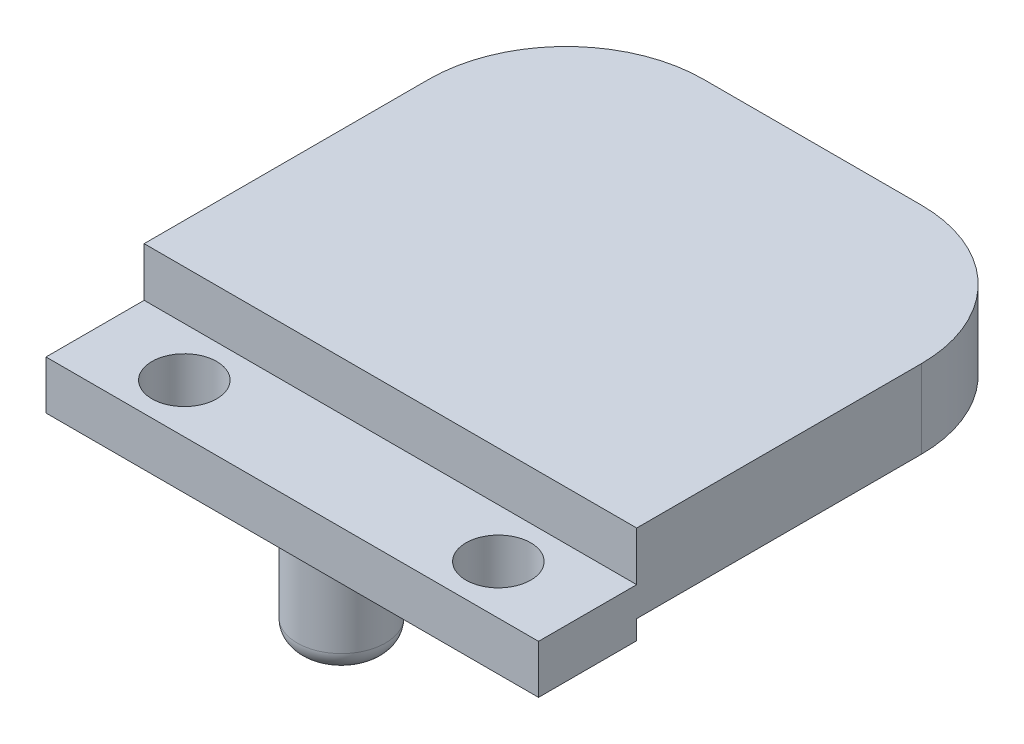
SolidWorks part; units mm, degrees
ref_plane "Front Plane" through (0, 0, 0) normal (0, 0, 1) x (1, 0, 0)
ref_plane "Top Plane" through (0, 0, 0) normal (0, 1, 0) x (1, 0, 0)
ref_plane "Right Plane" through (0, 0, 0) normal (1, 0, 0) x (0, 0, -1)
sketch "Sketch4" plane through (0, 0, 0) normal (0, 0, 1) x (1, 0, 0)
  line L1 (-6.23, -9.975) -> (6.23, -9.975)
  line L2 (-6.23, -9.975) -> (-6.23, 7.275)
  line L3 (-6.23, 7.275) -> (6.23, 7.275)
  line L4 (6.23, -9.975) -> (6.23, 7.275)
  point P4 (0, 7.275)
  dimension "D1" = 12.46
  dimension "D2" = 17.25
  dimension "D3" = 9.975
extrude "Boss-Extrude3" add sketch "Sketch4" along normal blind 6
sketch "Sketch8" plane through (0, -9.975, 0) normal (0, -1, 0) x (-1, 0, 0)
  circle A0 centre (0, -23.55) radius 12.5468
  circle A1 centre (0, -23.55) radius 11.15
  dimension "D1" = 22.3
  dimension "D2" = 23.55
extrude "Boss-Extrude6" add sketch "Sketch8" along normal blind 8.3 and the other way up to surface (17.25 mm away) other way up to face at (0, 7.275, 3)
sketch "Sketch5" plane through (0, 7.275, 0) normal (0, 1, 0) x (1, 0, 0)
  line L8 (12.5468, -23.55) -> (12.5468, 0)
  line L9 (12.5468, 0) -> (6.23, 0)
  line L10 (-12.5468, -23.55) -> (-12.5468, 0)
  line L11 (-12.5468, 0) -> (-6.23, 0)
  line L12 (-6.23, 0) -> (-6.23, -29.7)
  line L14 (6.23, -29.7) -> (6.23, 0)
  line L15 (-6.23, -29.7) -> (6.23, -29.7)
  line L16 (6.23, -6) -> (-6.23, -6) construction
  circle A0 centre (0, -23.55) radius 12.5468 construction
  arc A1 (-12.5468, -23.55) -> (12.5468, -23.55) centre (0, -23.55) ccw
  dimension "D1" = 23.7
  dimension "D2" = 23.55
extrude "Boss-Extrude4" add sketch "Sketch5" against normal up to surface (17.25 mm away) up to face at (0, -9.975, 3)
sketch "Sketch6" plane through (0, 7.275, 0) normal (0, 1, 0) x (1, 0, 0)
  line L0 (6.23, -6) -> (-6.23, -6) construction
  line L3 (6.23, -29.7) -> (-6.23, -29.7) construction
  circle A0 centre (0, -3.6) radius 0.75
  circle A1 centre (0, -32.1) radius 0.75
  dimension "D1" = 1.5
  dimension "D3" = 1.5
  dimension "D2" = 2.4
  dimension "D4" = 2.4
extrude "Cut-Extrude1" cut sketch "Sketch6" against normal blind 5
chamfer "Chamfer1" distance 0.5 angle 60 2 edges at (0, 7.275, 4.35) (0, 7.275, 32.85)
sketch "Sketch10" plane through (0, 7.275, 0) normal (0, 1, 0) x (1, 0, 0)
  line L1 (-6.23, -6) -> (6.23, -6)
  line L2 (-6.23, -6) -> (-6.23, -29.7)
  line L3 (-6.23, -29.7) -> (6.23, -29.7)
  line L4 (6.23, -6) -> (6.23, -29.7)
extrude "Cut-Extrude3" cut sketch "Sketch10" against normal up to surface (17.25 mm away) up to face at (0, -9.975, 10.3399)
ref_plane "Plane1" through (0, 0, 36.0968) normal (0, 0, 1) x (1, 0, 0)
sketch "Sketch13" plane through (0, -18.275, 0) normal (0, -1, 0) x (1, 0, 0)
  line L0 (-12.5468, 23.55) -> (-12.5468, 0)
  line L1 (-12.5468, 0) -> (12.5468, 0)
  line L2 (12.5468, 0) -> (12.5468, 23.55)
  arc A0 (-12.5468, 23.55) -> (12.5468, 23.55) centre (0, 23.55) ccw
  point P3 (0, 0)
extrude "Boss-Extrude7" add sketch "Sketch13" against normal up to surface (8.3 mm away) up to face at (0, -9.975, 10.3399)
sketch "Sketch15" plane through (0, 7.275, 0) normal (0, 1, 0) x (1, 0, 0)
  line L0 (-12.5468, 0) -> (12.5468, 0)
  line L1 (12.5468, 0) -> (12.5468, -23.55)
  line L2 (-12.5468, 0) -> (-12.5468, -23.55)
  line L3 (6.23, -6) -> (6.23, -29.7) construction
  line L4 (-6.23, -0.8) -> (6.23, -0.8)
  line L5 (-6.23, -0.8) -> (-6.23, -33)
  line L6 (-4.73, -34.5) -> (4.73, -34.5)
  line L7 (6.23, -0.8) -> (6.23, -33)
  arc A0 (-12.5468, -23.55) -> (12.5468, -23.55) centre (0, -23.55) ccw
  circle A1 centre (0, -3.6) radius 0.75 construction
  arc A2 (4.73, -34.5) -> (6.23, -33) centre (4.73, -33) ccw
  arc A3 (-6.23, -33) -> (-4.73, -34.5) centre (-4.73, -33) ccw
  point P15 (0, -0.8)
  dimension "D1" = 0.8
  dimension "D3" = 1.5
  dimension "D2" = 2.8
  dimension "D4" = 0
  dimension "D5" = 34.5
extrude "Boss-Extrude9" add sketch "Sketch15" along normal blind 10
sketch "Sketch20" plane through (0, -18.275, 0) normal (0, -1, 0) x (1, 0, 0)
  circle A0 centre (0, 23.55) radius 7.15
  circle A1 centre (0, 23.55) radius 11.15
  circle A2 centre (0, 23.55) radius 11.15 construction
  dimension "D1" = 14.3
extrude "Boss-Extrude11" add sketch "Sketch20" against normal up to surface (8.3 mm away) up to face at (0, -9.975, 27.1007)
sketch "Sketch21" plane through (0, -18.275, 0) normal (0, -1, 0) x (1, 0, 0)
  circle A0 centre (0, 23.55) radius 7.15
  circle A1 centre (0, 23.55) radius 10.15
  circle A2 centre (0, 23.55) radius 7.15 construction
  dimension "D1" = 20.3
extrude "Cut-Extrude7" cut sketch "Sketch21" against normal blind 1.3
sketch "Sketch11" plane through (0, 0, 29.7) normal (0, 0, 1) x (1, 0, 0)
  line L1 (-5, -9.975) -> (5, -9.975)
  line L2 (-5, -9.975) -> (-5, -11.975)
  line L3 (-5, -11.975) -> (5, -11.975)
  line L4 (5, -9.975) -> (5, -11.975)
  line L5 (3.6469, -9.975) -> (6.23, -9.975) construction
  point P4 (0, -9.975)
  dimension "D1" = 0
  dimension "D2" = 10
  dimension "D3" = 2
extrude "Cut-Extrude4" cut sketch "Sketch11" against normal up to surface (23.7 mm away) up to face at (0, -1.35, 6)
sketch "Sketch24" plane through (0, -18.275, 0) normal (0, -1, 0) x (1, 0, 0)
  line L0 (6.23, 20.0415) -> (6.23, 6) construction
  line L1 (-6.23, 6) -> (6.23, 6)
  line L2 (-6.23, 6) -> (-6.23, 12)
  line L3 (-6.23, 12) -> (6.23, 12)
  line L4 (6.23, 6) -> (6.23, 12)
  dimension "D1" = 6
extrude "Cut-Extrude8" cut sketch "Sketch24" against normal up to next
sketch "Sketch17" plane through (-12.5468, 4.7282, 0) normal (1, 0, 0) x (0, -1, 0)
  line L0 (26.9782, 26.5) -> (26.9782, 0)
  line L1 (26.9782, 0) -> (-17.5218, 0)
  line L2 (-17.5218, 0) -> (-17.5218, 26.5)
  line L3 (-17.5218, 26.5) -> (-13.5218, 26.5)
  line L4 (-13.5218, 26.5) -> (-13.5218, 5)
  line L5 (-13.5218, 5) -> (22.9782, 5)
  line L6 (22.9782, 5) -> (22.9782, 26.5)
  line L7 (22.9782, 26.5) -> (26.9782, 26.5)
  point P2 (4.7282, 5)
  point P10 (4.7282, 0)
  dimension "D1" = 4
  dimension "D2" = 36.5
  dimension "D3" = 0
  dimension "D4" = 26.5
  dimension "D5" = 5
extrude "Boss-Extrude10" add sketch "Sketch17" along normal up to surface (25.0936 mm away) up to face at (12.5468, -0.5, 11.775)
sketch "Sketch18" plane through (0, -18.25, 0) normal (0, 1, 0) x (0, 0, 1)
  line L0 (-26.5, -12.5468) -> (-26.5, 12.5468) construction
  line L1 (-26.5, 6.2191) -> (-5, 6.2191)
  line L2 (-26.5, 6.2191) -> (-26.5, -6.2191)
  line L3 (-26.5, -6.2191) -> (-5, -6.2191)
  line L4 (-5, 6.2191) -> (-5, -6.2191)
  line L5 (-5, -12.5468) -> (-5, 12.5468) construction
  point P6 (-26.5, 0)
  point P7 (-26.5, 0)
  dimension "D1" = 0
extrude "Cut-Extrude5" cut sketch "Sketch18" against normal blind 2
sketch "Sketch19" plane through (0, -20.25, 0) normal (0, 1, 0) x (0, 0, 1)
  line L0 (-26.5, -12.5468) -> (-26.5, 12.5468) construction
  line L1 (-26.5, 12.5468) -> (-26.5, -12.5468) construction
  circle A0 centre (-20, 0) radius 3.5
  point P8 (-26.5, 0)
  dimension "D1" = 7
  dimension "D2" = 6.5
extrude "Cut-Extrude6" cut sketch "Sketch19" against normal through all both and the other way through all
fillet "Fillet1" radius 7 4 edges at (12.5468, -20.25, -26.5) (-12.5468, -20.25, -26.5) (-12.5468, 20.25, -26.5) (12.5468, 20.25, -26.5)
ref_plane "Plane2" through (0, 0, 0) normal (1, 0, 0) x (0, 0, -1)
ref_plane "Plane3" through (0, -0.5, 0) normal (0, -1, 0) x (-1, 0, 0)
sketch "Sketch22" plane through (0, 22.25, 0) normal (0, 1, 0) x (1, 0, 0)
  circle A0 centre (0, 20) radius 6.5
  dimension "D1" = 13
extrude "Boss-Extrude12" add sketch "Sketch22" against normal blind 5
sketch "Sketch23" plane through (0, 17.25, 0) normal (0, -1, 0) x (1, 0, 0)
  circle A0 centre (0, -20) radius 6.075
  dimension "D1" = 12.15
extrude "Boss-Extrude13" add sketch "Sketch23" along normal blind 5
fillet "Fillet2" radius 1 1 edges at (0, 12.25, -26.075)
sketch "Sketch25" plane through (0, -20.25, 0) normal (0, 1, 0) x (1, 0, 0)
  line L0 (-6.2191, 5) -> (-2.5, 5)
  line L1 (12.5468, 5) -> (-12.5468, 5) construction
  line L2 (-2.5, 5) -> (-3.1585, 20)
  line L3 (-3.1585, 20) -> (-3.4438, 26.5)
  line L4 (-3.4438, 26.5) -> (-6.2191, 26.5)
  line L5 (-6.2191, 26.4676) -> (-6.2191, 5) construction
  line L6 (-6.2191, 26.5) -> (-6.2191, 5)
  line L7 (6.2191, 5) -> (2.5, 5)
  line L8 (2.5, 5) -> (3.1585, 20)
  line L9 (3.1585, 20) -> (3.4438, 26.5)
  line L10 (3.4438, 26.5) -> (6.2191, 26.5)
  line L11 (6.2191, 5) -> (6.2191, 26.4676) construction
  line L12 (6.2191, 26.5) -> (6.2191, 5)
  line L13 (0, -23.6775) -> (0, 23.6775) construction
  line L14 (5.5468, 26.5) -> (-5.5468, 26.5) construction
  circle A0 centre (0, 20) radius 3.5 construction
  dimension "D1" = 5
  dimension "D2" = 2.5
  dimension "D3" = 3.1585
  dimension "D4" = 6.317
  dimension "D5" = 0
  dimension "D6" = 0
extrude "Boss-Extrude15" add sketch "Sketch25" along normal up to surface (2 mm away) up to face at (9.7194, -18.25, -14.2975)
sketch "Sketch26" plane through (0, -22.25, 0) normal (0, -1, 0) x (-1, 0, 0)
  circle A0 centre (0, 10) radius 0.75
  circle A1 centre (0, 20) radius 3.5 construction
  dimension "D1" = 1.5
  dimension "D2" = 10
  dimension "D3" = 0
extrude "Cut-Extrude9" cut sketch "Sketch26" against normal up to next
sketch "Sketch27" plane through (-12.5468, 0, 0) normal (-1, 0, 0) x (0, 0, 1)
  line L0 (36.0968, 17.275) -> (-10.0207, 17.275)
  line L1 (-10.0207, 17.275) -> (-10.0207, 5.3316)
  line L2 (-10.0207, 5.3316) -> (-33.3295, 5.3316)
  line L3 (-33.3295, 5.3316) -> (-33.3295, -27.205)
  line L4 (-33.3295, -27.205) -> (36.0968, -27.205)
  line L5 (36.0968, -27.205) -> (36.0968, 17.275)
extrude "Cut-Extrude10" cut sketch "Sketch27" against normal through all
sketch "Sketch28" plane through (0, 17.275, 0) normal (0, -1, 0) x (1, 0, 0)
  line L0 (0, -2.7363) -> (0, 2.7363) construction
  line L1 (12.5468, 0) -> (-12.5468, 0) construction
  circle A0 centre (-8, -2.5) radius 1.65
  circle A1 centre (8, -2.5) radius 1.65
  dimension "D1" = 3.3
  dimension "D2" = 3.3
  dimension "D3" = 16
  dimension "D4" = 8
  dimension "D5" = 2.5
extrude "Cut-Extrude11" cut sketch "Sketch28" against normal through all
sketch "Sketch29" plane through (0, 17.275, 0) normal (0, -1, 0) x (1, 0, 0)
  line L0 (0, -2.7363) -> (0, 2.7363) construction
  circle A0 centre (0, -2.5) radius 2.25
  circle A1 centre (-8, -2.5) radius 1.65 construction
  dimension "D2" = 4.5
  dimension "D1" = 0
extrude "Boss-Extrude16" add sketch "Sketch29" along normal blind 5
fillet "Fillet3" radius 1 1 edges at (0, 12.275, -4.75)
sketch "Sketch30" plane through (12.5468, 0, 0) normal (1, 0, 0) x (0, 0, -1)
  line L1 (0, 22.25) -> (5, 22.25)
  line L2 (0, 22.25) -> (0, 19.75)
  line L3 (0, 19.75) -> (5, 19.75)
  line L4 (5, 22.25) -> (5, 19.75)
  dimension "D1" = 2.5
extrude "Cut-Extrude12" cut sketch "Sketch30" against normal through all
